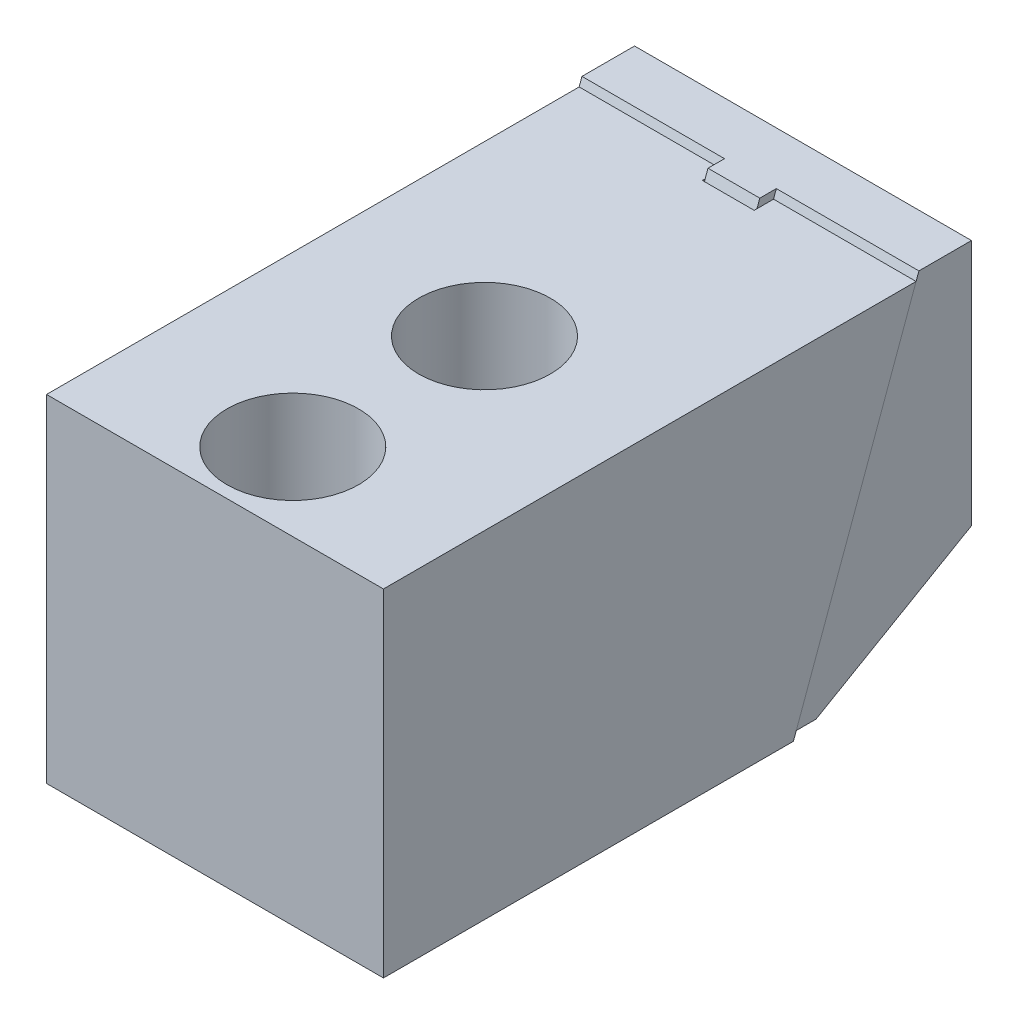
SolidWorks part; units mm, degrees
material "Alloy Steel"
ref_plane "Front Plane" through (0, 0, 0) normal (0, 0, 1) x (1, 0, 0)
ref_plane "Top Plane" through (0, 0, 0) normal (0, 1, 0) x (1, 0, 0)
ref_plane "Right Plane" through (0, 0, 0) normal (1, 0, 0) x (0, 0, -1)
sketch "Sketch1" plane through (0, 0, 0) normal (1, 0, 0) x (0, 0, -1)
  line L0 (0, 65.024) -> (0, 0)
  line L1 (0, 0) -> (79.127, 0)
  line L2 (79.127, 0) -> (102.7938, 65.024)
  line L3 (102.7938, 65.024) -> (0, 65.024)
  dimension "D1" = 65.024
  dimension "D2" = 102.7938
  dimension "D3" = 20
extrude "Extrude1" add sketch "Sketch1" along normal mid plane 65.024
sketch "Sketch2" plane through (0, 0, 0) normal (1, 0, 0) x (0, 0, -1)
  line L0 (99.06, 65.024) -> (75.3932, 0)
  line L1 (99.06, 65.024) -> (102.7938, 65.024)
  line L2 (102.7938, 65.024) -> (79.127, 0)
  line L3 (79.127, 0) -> (75.3932, 0)
  line L4 (0, 0) -> (79.127, 0) construction
  line L5 (102.7938, 65.024) -> (0, 65.024) construction
  line L6 (79.127, 0) -> (102.7938, 65.024) construction
  dimension "D1" = 3.7338
extrude "Cut-Extrude1" cut sketch "Sketch2" against normal mid plane 10.0076
hole_wizard "Hole1" positions "Sketch6" profile "Sketch5" legacy end condition up to next
sketch "Sketch6" plane through (0, 65.024, 0) normal (0, 1, 0) x (-1, 0, 0)
  line L0 (-32.512, 0) -> (32.512, 0) construction
  point P0 (0, -15.0114)
  point P1 (0, -52.0192)
  dimension "D1" = 15.0114
  dimension "D2" = 37.0078
sketch "Sketch5" plane through (0, 65.024, -15.0114) normal (1, 0, 0) x (0, 0, 1)
  line L0 (0, 0) -> (0, 65.024)
  line L1 (0, 65.024) -> (8.255, 65.024)
  line L2 (8.255, 65.024) -> (8.255, 18.034)
  line L3 (8.255, 18.034) -> (12.7, 18.034)
  line L4 (12.7, 18.034) -> (12.7, 0)
  line L5 (12.7, 0) -> (0, 0)
  line L6 (0, 110) -> (0, -10) construction
  dimension "Diameter" = 16.51
  dimension "Depth" = 65.024
  dimension "C-Bore Diameter" = 25.4
  dimension "C-Bore Depth" = 18.034
sketch "Sketch7" plane through (0, 0, 0) normal (1, 0, 0) x (0, 0, -1)
  line L0 (79.6803, 1.5202) -> (83.4832, 1.5202)
  line L1 (83.4832, 1.5202) -> (113.4872, 18.843)
  line L2 (113.4872, 18.843) -> (113.4872, 66.5188)
  line L3 (113.4872, 66.5188) -> (103.3379, 66.5188)
  line L4 (103.3379, 66.5188) -> (79.6803, 1.5202)
  line L5 (79.127, 0) -> (102.7938, 65.024) construction
  line L6 (0, 0) -> (79.127, 0) construction
  line L7 (0, 65.024) -> (0, 0) construction
  dimension "D2" = 1.5202
  dimension "D3" = 113.4872
  dimension "D4" = 64.9986
  dimension "D5" = 17.3228
  dimension "D6" = 30
  dimension "D7" = 10.1493
extrude "Extrude2" add sketch "Sketch7" along normal mid plane 65.024 separate body
sketch "Sketch8" plane through (0, 0, 0) normal (1, 0, 0) x (0, 0, -1)
  line L0 (103.3379, 66.5188) -> (100.1453, 66.5188)
  line L1 (100.1453, 66.5188) -> (76.4878, 1.5202)
  line L2 (76.4878, 1.5202) -> (79.6803, 1.5202)
  line L3 (103.3379, 66.5188) -> (79.6803, 1.5202) construction
  line L4 (103.3379, 66.5188) -> (79.6803, 1.5202)
  dimension "D1" = 3
extrude "Extrude3" add sketch "Sketch8" along normal mid plane 10
sketch "Sketch9" plane through (0, 0, 0) normal (1, 0, 0) x (0, 0, -1)
  line L0 (47.4312, 31.0202) -> (86.4656, 31.0202) construction
  line L1 (113.4872, 18.843) -> (113.4872, 66.5188) construction
  line L2 (76.1873, 31.0202) -> (113.4872, 31.0202)
  line L3 (76.1873, 31.0202) -> (76.1873, 44.0202)
  line L4 (76.1873, 44.0202) -> (101.5873, 44.0202)
  line L5 (101.5873, 34.1203) -> (101.5873, 44.0202)
  line L6 (79.6803, 1.5202) -> (83.4832, 1.5202) construction
  line L7 (101.5873, 34.1203) -> (106.1872, 34.1203)
  line L8 (106.1872, 34.1203) -> (106.1872, 36.5203)
  line L9 (106.1872, 36.5203) -> (113.4872, 36.5203)
  line L10 (113.4872, 36.5203) -> (113.4872, 31.0202)
  dimension "D1" = 11.8999
  dimension "D2" = 26
  dimension "D3" = 29.5
  dimension "D4" = 6.2001
  dimension "D5" = 7.3
  dimension "D6" = 11.0002
  dimension "D7" = 25.4
revolve "Cut-Revolve1" cut sketch "Sketch9" angle 360 about L0
sketch "Sketch10" plane through (0, 0, -106.1872) normal (0, 0, -1) x (-1, 0, 0)
  circle A0 centre (0, 31.0202) radius 5
  dimension "D1" = 10
extrude "Extrude4" add sketch "Sketch10" along normal blind 6
sketch "Sketch11" plane through (0, 0, -112.1872) normal (0, 0, -1) x (-1, 0, 0)
  line L1 (1.7321, 28.0202) -> (3.4641, 31.0202)
  line L2 (3.4641, 31.0202) -> (1.7321, 34.0202)
  line L3 (1.7321, 34.0202) -> (-1.7321, 34.0202)
  line L4 (-1.7321, 34.0202) -> (-3.4641, 31.0202)
  line L5 (-3.4641, 31.0202) -> (-1.7321, 28.0202)
  line L6 (-1.7321, 28.0202) -> (1.7321, 28.0202)
  circle A0 centre (0, 31.0202) radius 3 construction
  dimension "D1" = 6
extrude "Cut-Extrude2" cut sketch "Sketch11" against normal up to surface (6 mm away) up to face at (5.5001, 31.0202, -106.1872)
sketch "Sketch12" plane through (0, 0, 0) normal (0, -1, 0) x (1, 0, 0)
  circle A0 centre (0, -52.0192) radius 16.002
  dimension "D1" = 32.004
extrude "Cut-Extrude3" cut sketch "Sketch12" against normal blind 5.842
